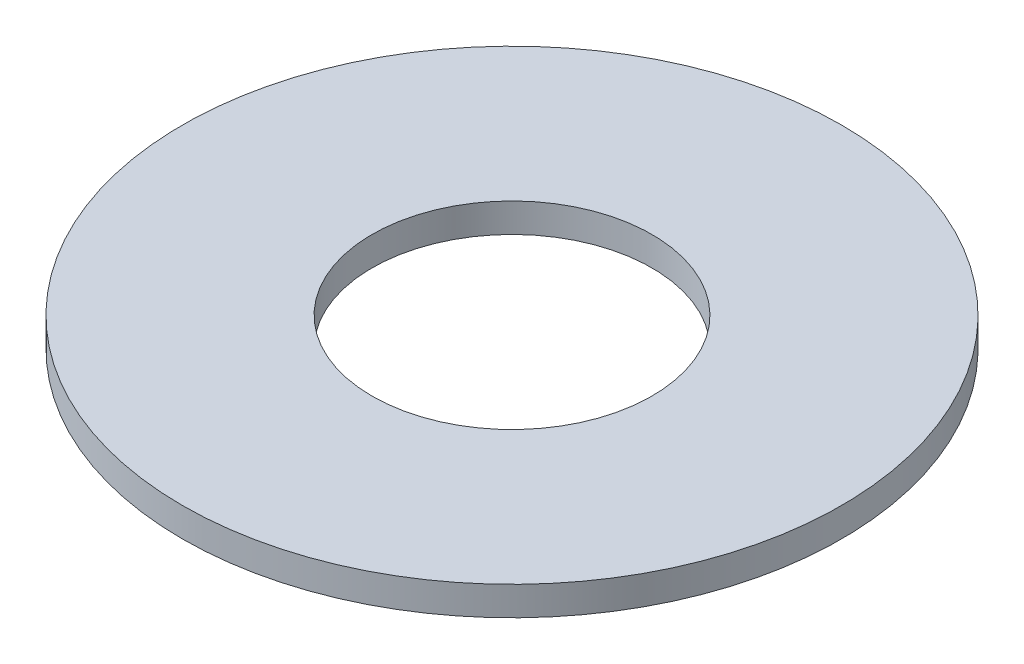
SolidWorks part; units mm, degrees
ref_plane "Front Plane" through (0, 0, 0) normal (0, 0, 1) x (1, 0, 0)
ref_plane "Top Plane" through (0, 0, 0) normal (0, 1, 0) x (1, 0, 0)
ref_plane "Right Plane" through (0, 0, 0) normal (1, 0, 0) x (0, 0, -1)
sketch "Sketch1" plane through (0, 0, 0) normal (0, 1, 0) x (1, 0, 0)
  circle A0 centre (0, 0) radius 15.875
  dimension "OD" = 31.75
extrude "Boss-Extrude1" add sketch "Sketch1" along normal blind 1.397
sketch "Sketch5" plane through (0, 1.397, 0) normal (0, 1, 0) x (-1, 0, 0)
  circle A0 centre (0, 0) radius 6.7437
  dimension "ID" = 13.4874
extrude "Cut-Extrude1" cut sketch "Sketch5" against normal through all
